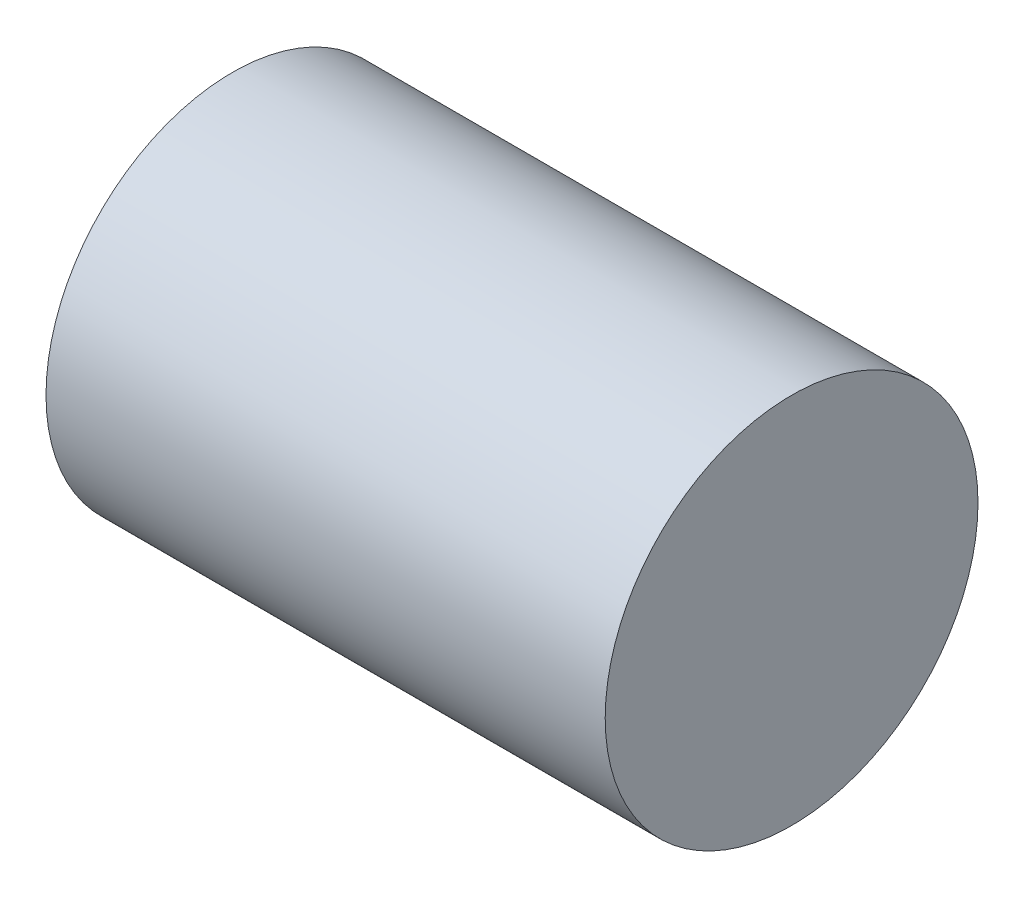
SolidWorks part; units mm, degrees
ref_plane "前基準面" through (0, 0, 0) normal (0, 0, 1) x (1, 0, 0)
ref_plane "上基準面" through (0, 0, 0) normal (0, 1, 0) x (1, 0, 0)
ref_plane "右基準面" through (0, 0, 0) normal (1, 0, 0) x (0, 0, -1)
sketch "草圖1" plane through (0, 0, 0) normal (1, 0, 0) x (0, 0, -1)
  circle A0 centre (0, 0) radius 2
  dimension "D1" = 4
extrude "填料-伸長1" add sketch "草圖1" along normal mid plane 6
